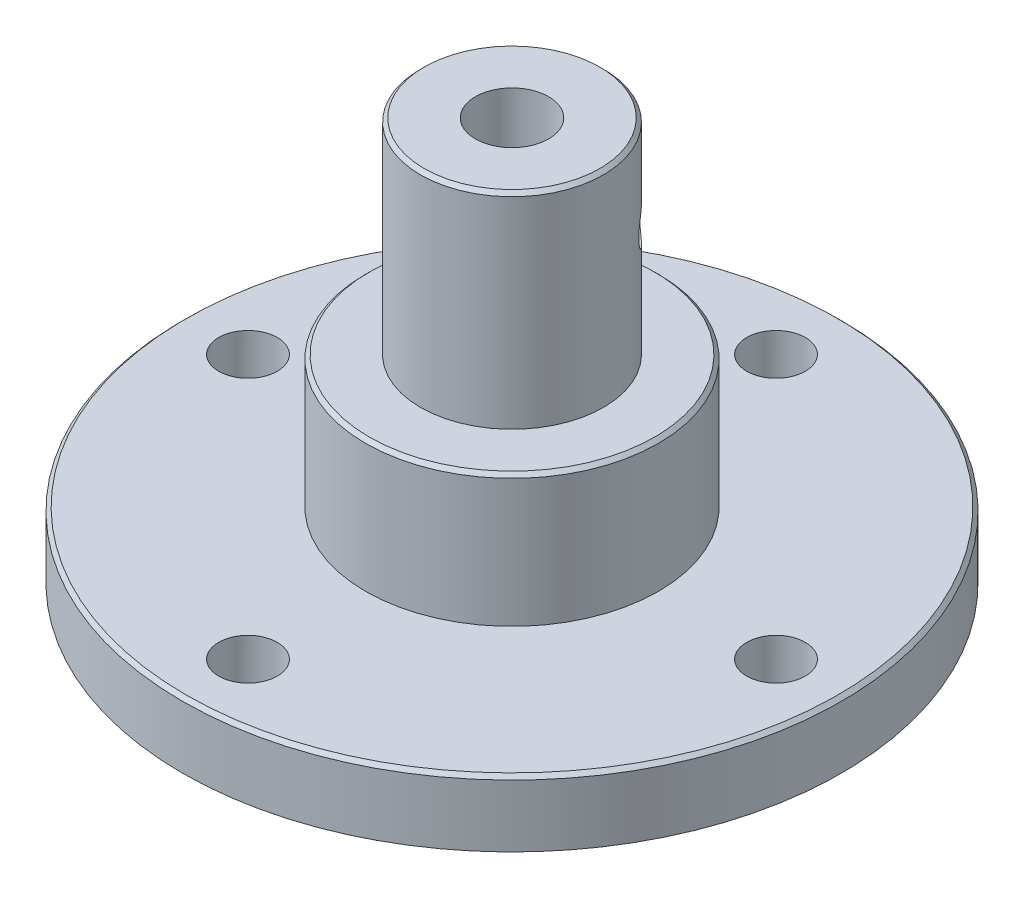
SolidWorks part; units mm, degrees
material "1.0037 (S235JR)"
ref_plane "Front Plane" through (0, 0, 0) normal (0, 0, 1) x (1, 0, 0)
ref_plane "Top Plane" through (0, 0, 0) normal (0, 1, 0) x (1, 0, 0)
ref_plane "Right Plane" through (0, 0, 0) normal (1, 0, 0) x (0, 0, -1)
sketch "Sketch1" plane through (0, 0, 0) normal (0, 1, 0) x (1, 0, 0)
  circle A0 centre (0, 0) radius 45
extrude "Boss-Extrude1" add sketch "Sketch1" along normal blind 9
sketch "Sketch3" plane through (0, 9, 0) normal (0, 1, 0) x (1, 0, 0)
  circle A0 centre (0, 0) radius 20
extrude "Boss-Extrude2" add sketch "Sketch3" along normal blind 18
sketch "Sketch4" plane through (0, 27, 0) normal (0, 1, 0) x (1, 0, 0)
  circle A0 centre (0, 0) radius 12.5
extrude "Boss-Extrude3" add sketch "Sketch4" along normal blind 28
sketch "Sketch5" plane through (0, 0, 0) normal (0, -1, 0) x (1, 0, 0)
  circle A0 centre (0, 0) radius 28.5
extrude "Boss-Extrude4" add sketch "Sketch5" along normal blind 2
sketch "Sketch6" plane through (0, 55, 0) normal (0, 1, 0) x (1, 0, 0)
  circle A0 centre (0, 0) radius 5
extrude "Cut-Extrude1" cut sketch "Sketch6" against normal blind 40
sketch "Sketch7" plane through (0, 0, 0) normal (1, 0, 0) x (0, 0, -1)
  line L1 (0, -2) -> (-15, -2)
  line L2 (-28.5, -2) -> (28.5, -2) construction
  line L3 (-15, -2) -> (-15, 4)
  line L6 (0, -2) -> (0, 13)
  spline S0 degree 2 poles (-15, 4) (-8.5602, 11.2048) (0, 13) knots 0 0 0 1 1 1
revolve "Cut-Revolve1" cut sketch "Sketch7" angle 360 about L6
sketch "Sketch8" plane through (0, 0, 0) normal (0, -1, 0) x (1, 0, 0)
  circle A0 centre (0, 0) radius 36.05
  circle A1 centre (0, 36.05) radius 4
  circle A2 centre (-36.05, 0) radius 4
  circle A3 centre (0, -36.05) radius 4
  circle A4 centre (36.05, 0) radius 4
  dimension "D1" = 72.1
extrude "Cut-Extrude2" cut sketch "Sketch8" against normal up to next contours A0 A4 | A0 A4 | A0 A1 | A0 A1 | A0 A2 | A0 A2 | A0 A3 | A0 A3
ref_plane "Plane1" through (8.8388, 0, -8.8388) normal (-0.7071, 0, 0.7071) x (0, -1, 0)
sketch "Sketch9" plane through (8.8388, 0, -8.8388) normal (-0.7071, 0, 0.7071) x (0, -1, 0)
  circle A0 centre (-42.5, 0) radius 2.5
extrude "Cut-Extrude3" cut sketch "Sketch9" along normal up to surface (8.1699 mm away)
chamfer "Chamfer1" distance 0.5 angle 45 3 edges at (0, 27, 20) (0, 9, 45) (0, 55, 12.5)
